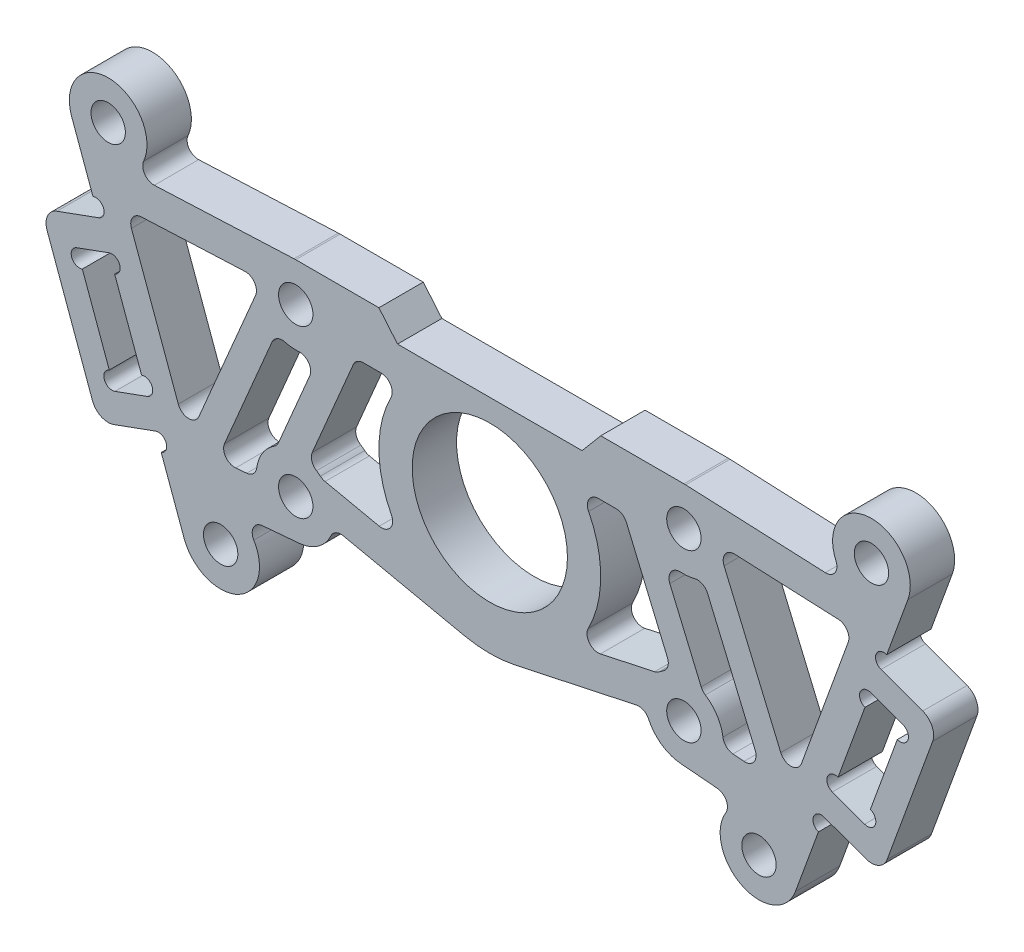
SolidWorks part; units mm, degrees
ref_plane "前视基准面" through (0, 0, 0) normal (0, 0, 1) x (1, 0, 0)
ref_plane "上视基准面" through (0, 0, 0) normal (0, 1, 0) x (1, 0, 0)
ref_plane "右视基准面" through (0, 0, 0) normal (1, 0, 0) x (0, 0, -1)
sketch "草图1" plane through (0, 0, 0) normal (0, 0, 1) x (1, 0, 0)
  line L0 (-17.5, 11) -> (-10, 11)
  line L1 (17.5, -7.5) -> (-17.5, -7.5) construction
  line L2 (17.5, -7.5) -> (17.5, 7.5) construction
  line L3 (17.5, 7.5) -> (-17.5, 7.5) construction
  line L4 (-17.5, -7.5) -> (-17.5, 7.5) construction
  line L5 (17.5, -7.5) -> (-17.5, 7.5) construction
  line L6 (17.5, 7.5) -> (-17.5, -7.5) construction
  line L7 (-10, 11) -> (-8.3218, 9)
  line L8 (-8.3218, 9) -> (8.3218, 9)
  line L9 (8.3218, 9) -> (10, 11)
  line L10 (10, 11) -> (17.5, 11)
  line L11 (-14.0777, -8.2333) -> (-2.3046, -10.7559)
  line L12 (-17.6552, 10.9966) -> (-37, 10.1377)
  line L13 (14.0777, -8.2333) -> (2.3046, -10.7559)
  line L14 (-37, 10.1377) -> (-28.9425, -12)
  line L15 (-28.9425, -12) -> (-17.1992, -10.9871)
  line L16 (17.6552, 10.9966) -> (37, 10.1377)
  line L17 (37, 10.1377) -> (28.9425, -12)
  line L18 (28.9425, -12) -> (17.1992, -10.9871)
  line L19 (-37, 10.1377) -> (-38.9566, 15.5135) construction
  line L20 (-38.9566, 15.5135) -> (-41.7757, 14.4874) construction
  line L21 (-41.7757, 14.4874) -> (-29.805, -18.4018) construction
  line L22 (-29.805, -18.4018) -> (-26.9859, -17.3758) construction
  line L23 (-26.9859, -17.3758) -> (-28.9425, -12) construction
  line L28 (-38.6034, 5.7716) -> (-48.0003, 2.3514) construction
  line L29 (-32.447, -11.1429) -> (-41.844, -14.5631) construction
  line L30 (-48.0003, 2.3514) -> (-41.844, -14.5631) construction
  line L31 (-41.844, -14.5631) -> (-44.663, -15.5892) construction
  line L32 (-44.663, -15.5892) -> (-50.8194, 1.3253) construction
  line L33 (-50.8194, 1.3253) -> (-48.0003, 2.3514) construction
  line L34 (-51.5, -8.5) -> (-44.9222, -6.1059) construction
  line L35 (0, 9) -> (0, -11) construction
  line L36 (41.7757, 14.4874) -> (29.805, -18.4018) construction
  line L37 (37, 10.1377) -> (38.9566, 15.5135) construction
  line L38 (38.9566, 15.5135) -> (41.7757, 14.4874) construction
  line L39 (50.8194, 1.3253) -> (48.0003, 2.3514) construction
  line L40 (38.6034, 5.7716) -> (48.0003, 2.3514) construction
  line L41 (44.663, -15.5892) -> (50.8194, 1.3253) construction
  line L42 (41.844, -14.5631) -> (44.663, -15.5892) construction
  line L43 (48.0003, 2.3514) -> (41.844, -14.5631) construction
  line L44 (32.447, -11.1429) -> (41.844, -14.5631) construction
  line L45 (26.9859, -17.3758) -> (28.9425, -12) construction
  line L46 (29.805, -18.4018) -> (26.9859, -17.3758) construction
  line L47 (44.9222, -6.1059) -> (32.7061, -1.6596) construction
  circle A0 centre (0, 0) radius 7
  circle A2 centre (17.5, 7.5) radius 1.55
  circle A3 centre (17.5, -7.5) radius 1.55
  circle A4 centre (-17.5, -7.5) radius 1.55
  circle A5 centre (-17.5, 7.5) radius 1.55
  arc A6 (-17.5, 11) -> (-17.6552, 10.9966) centre (-17.5, 7.5) ccw
  arc A7 (-17.1992, -10.9871) -> (-14.0777, -8.2333) centre (-17.5, -7.5) ccw
  arc A8 (14.0777, -8.2333) -> (17.1992, -10.9871) centre (17.5, -7.5) ccw
  arc A9 (17.6552, 10.9966) -> (17.5, 11) centre (17.5, 7.5) ccw
  arc A10 (-2.3046, -10.7559) -> (2.3046, -10.7559) centre (0, 0) ccw
  circle A11 centre (-51.5, -8.5) radius 4 construction
  circle A12 centre (51.5, -8.5) radius 4 construction
  dimension "D1" = 14
  dimension "D2" = 11
  dimension "D4" = 3.1
  dimension "D6" = 7
  dimension "D18" = 8
  dimension "D19" = 8.5
  dimension "D10" = 103
  dimension "D3" = 35
  dimension "D5" = 15
  dimension "D7" = 2
  dimension "D8" = 20
  dimension "D9" = 50
  dimension "D11" = 70
  dimension "D12" = 74
  dimension "D13" = 12
  dimension "D14" = 3
  dimension "D15" = 10
  dimension "D16" = 18
  dimension "D17" = 3
  dimension "D20" = 35
extrude "凸台-拉伸1" add sketch "草图1" along normal mid plane 4
fillet "圆角1" radius 1 2 edges at (14.0777, -8.2333, 0) (-14.0777, -8.2333, 0)
sketch "草图2" plane through (0, 0, 2) normal (0, 0, 1) x (1, 0, 0)
  line L0 (-20.5, 7.8673) -> (-32.7826, 7.322)
  line L1 (-32.7826, 7.322) -> (-27.2229, -7.9533)
  line L2 (-27.2229, -7.9533) -> (-20.5, 7.8673)
  line L3 (-19.2518, 4.4123) -> (-24.5732, -8.1101)
  line L4 (-24.5732, -8.1101) -> (-21.0369, -7.8051)
  line L5 (-19.1827, -4.3741) -> (-15.3311, 4.6896)
  line L6 (-17.6552, 10.9966) -> (-37, 10.1377) construction
  line L7 (-37, 10.1377) -> (-28.9425, -12) construction
  line L8 (-28.9425, -12) -> (-17.1992, -10.9871) construction
  arc A0 (-21.0369, -7.8051) -> (-19.1827, -4.3741) centre (-17.5, -7.5) cw
  circle A1 centre (-17.5, -7.5) radius 1.55 construction
  arc A2 (-19.2518, 4.4123) -> (-15.3311, 4.6896) centre (-17.5, 7.5) ccw
  circle A3 centre (-17.5, 7.5) radius 1.55 construction
  circle A4 centre (-17.5, 7.5) radius 1.55 construction
  dimension "D1" = 2
  dimension "D2" = 2
  dimension "D6" = 3.5
  dimension "D7" = 3
  dimension "D3" = 3
  dimension "D4" = 3
  dimension "D5" = 2.5
extrude "切除-拉伸1" cut sketch "草图2" against normal through all both and the other way through all
fillet "圆角2" radius 1 8 edges at (-19.2518, 4.4123, 0) (-21.0369, -7.8051, 0) (-19.1827, -4.3741, 0) (-15.3311, 4.6896, 0) (-24.5732, -8.1101, 0) (-27.2229, -7.9533, 0) (-32.7826, 7.322, 0) (-20.5, 7.8673, 0)
mirror "镜向1" about plane through (0, 0, 0) normal (1, 0, 0) of "圆角2", "切除-拉伸1"
sketch "草图3" plane through (0, 0, 2) normal (0, 0, 1) x (1, 0, 0)
  line L0 (-17.6552, 10.9966) -> (-37, 10.1377) construction
  line L1 (-37, 10.1377) -> (-28.9425, -12) construction
  line L2 (-28.9425, -12) -> (-17.1992, -10.9871) construction
  line L3 (-37.6991, 12.0585) -> (-37, 10.1377)
  line L4 (-37, 10.1377) -> (-32.4761, 10.3385)
  line L5 (-27.5576, -15.8051) -> (-28.9425, -12)
  line L6 (-28.9425, -12) -> (-22.7304, -11.4642)
  circle A0 centre (-34.4102, 13.2556) radius 1.55
  circle A1 centre (-24.2687, -14.608) radius 1.55
  arc A2 (-32.4761, 10.3385) -> (-37.6991, 12.0585) centre (-34.4102, 13.2556) ccw
  arc A3 (-27.5576, -15.8051) -> (-22.7304, -11.4642) centre (-24.2687, -14.608) ccw
  dimension "D1" = 3.1
  dimension "D2" = 3
  dimension "D3" = 7
  dimension "D4" = 3
extrude "凸台-拉伸2" add sketch "草图3" against normal up to surface (4 mm away) up to face at (26.873, 2.7167, -2)
mirror "镜向2" about plane through (0, 0, 0) normal (1, 0, 0) of "凸台-拉伸2"
fillet "圆角3" radius 1 4 edges at (-22.7304, -11.4642, 0) (-32.4761, 10.3385, 0) (32.4761, 10.3385, 0) (22.7304, -11.4642, 0)
sketch "草图4" plane through (0, 0, 2) normal (0, 0, 1) x (1, 0, 0)
  line L0 (-16.3849, -4.1824) -> (-12.0579, 6)
  line L1 (-12.0579, 6) -> (-8, 6)
  line L2 (-15.1087, -4.9443) -> (-7.5429, -6.5654)
  line L3 (-13.2099, -8.4192) -> (-2.3046, -10.7559) construction
  line L4 (8.3218, 9) -> (-8.3218, 9) construction
  line L5 (-19.0548, -4.0732) -> (-16.2308, 2.5723) construction
  arc A0 (-8, 6) -> (-7.5429, -6.5654) centre (0, 0) ccw
  circle A1 centre (0, 0) radius 7 construction
  arc A2 (-15.1087, -4.9443) -> (-16.3849, -4.1824) centre (-17.5, -7.5) ccw
  dimension "D1" = 3
  dimension "D2" = 2.5
  dimension "D3" = 3
  dimension "D4" = 3
extrude "切除-拉伸2" cut sketch "草图4" against normal through all
mirror "镜向3" about plane through (0, 0, 0) normal (1, 0, 0) of "切除-拉伸2"
fillet "圆角4" radius 1 10 edges at (-12.0579, 6, 0) (-8, 6, 0) (-7.5429, -6.5654, 0) (-15.1087, -4.9443, 0) (-16.3849, -4.1824, 0) (8, 6, 0) (12.0579, 6, 0) (16.3849, -4.1824, 0) (15.1087, -4.9443, 0) (7.5429, -6.5654, 0)
sketch "草图5" plane through (0, 0, 2) normal (0, 0, 1) x (1, 0, 0)
  line L0 (44.9222, -6.1059) -> (32.7061, -1.6596) construction
  line L1 (30.885, -6.3708) -> (33.798, -7.4311)
  line L2 (30.885, -6.3708) -> (34.3394, 3.1201)
  line L3 (34.3394, 3.1201) -> (37.2524, 2.0598)
  line L4 (33.798, -7.4311) -> (37.2524, 2.0598)
  line L5 (30.885, -6.3708) -> (37.2524, 2.0598) construction
  line L6 (34.3394, 3.1201) -> (33.798, -7.4311) construction
  line L7 (37, 10.1377) -> (28.9425, -12) construction
  point P0 (34.0687, -2.1555)
  dimension "D1" = 3
  dimension "D2" = 3.1
  dimension "D3" = 10.1
extrude "切除-拉伸3" cut sketch "草图5" against normal through all
sketch "草图7" plane through (0, 0, 2) normal (0, 0, 1) x (1, 0, 0)
  line L0 (35.2713, 5.3881) -> (40.4396, 3.507)
  line L1 (34.4333, 3.0859) -> (37.6991, 12.0585) construction
  line L2 (40.4396, 3.507) -> (35.3093, -10.5884)
  line L3 (35.3093, -10.5884) -> (30.141, -8.7073)
  line L4 (27.5576, -15.8051) -> (30.9789, -6.405) construction
  line L5 (30.141, -8.7073) -> (30.9789, -6.405)
  line L6 (30.9789, -6.405) -> (33.798, -7.4311)
  line L7 (33.798, -7.4311) -> (37.2524, 2.0598)
  line L8 (37.2524, 2.0598) -> (34.4333, 3.0859)
  line L9 (34.4333, 3.0859) -> (35.2713, 5.3881)
  dimension "D1" = 15
  dimension "D2" = 2.5
extrude "凸台-拉伸3" add sketch "草图7" against normal up to surface (4 mm away)
mirror "镜向4" about plane through (0, 0, 0) normal (1, 0, 0) of "凸台-拉伸3", "切除-拉伸3"
sketch "草图8" plane through (0, 0, -2) normal (0, 0, -1) x (-1, 0, 0)
  line L0 (-33.798, -7.4311) -> (-37.2524, 2.0598) construction
  line L1 (-34.3394, 3.1201) -> (-30.885, -6.3708) construction
  line L2 (-35.2713, 5.3881) -> (-37.6991, 12.0585) construction
  line L3 (-27.5576, -15.8051) -> (-30.141, -8.7073) construction
  circle A0 centre (-36.9959, 1.355) radius 0.75
  circle A1 centre (-34.0829, 2.4153) radius 0.75
  circle A2 centre (-34.0545, -6.7263) radius 0.75
  circle A3 centre (-31.1415, -5.6661) radius 0.75
  circle A4 centre (-35.5278, 6.0929) radius 0.75
  circle A5 centre (-29.8845, -9.4121) radius 0.75
  dimension "D1" = 1.5
extrude "切除-拉伸4" cut sketch "草图8" against normal through all
mirror "镜向5" about plane through (0, 0, 0) normal (1, 0, 0) of "切除-拉伸4"
fillet "圆角5" radius 1.5 4 edges at (40.4396, 3.507, 0) (35.3093, -10.5884, 0) (-40.4396, 3.507, 0) (-35.3093, -10.5884, 0)
